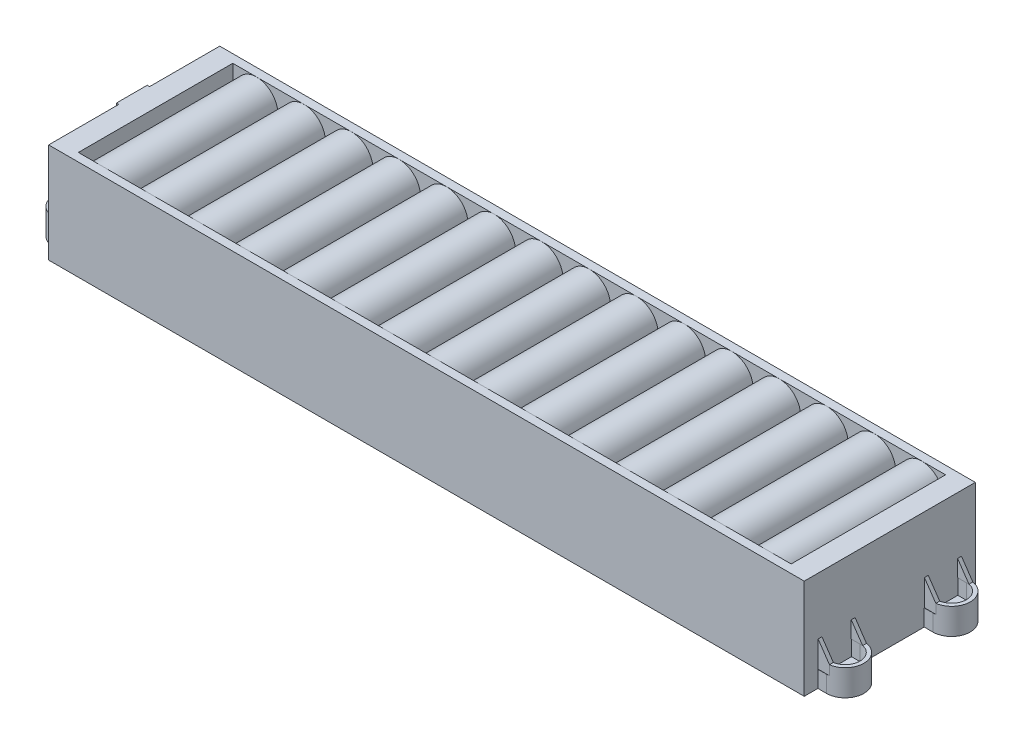
SolidWorks part; units mm, degrees
ref_plane "Front Plane" through (0, 0, 0) normal (0, 0, 1) x (1, 0, 0)
ref_plane "Top Plane" through (0, 0, 0) normal (0, 1, 0) x (1, 0, 0)
ref_plane "Right Plane" through (0, 0, 0) normal (1, 0, 0) x (0, 0, -1)
sketch "Sketch1" plane through (0, 0, 0) normal (0, 1, 0) x (1, 0, 0)
  line L1 (159, -36) -> (-159, -36)
  line L2 (159, -36) -> (159, 36)
  line L3 (159, 36) -> (-159, 36)
  line L4 (-159, -36) -> (-159, 36)
  line L5 (159, -36) -> (-159, 36) construction
  line L6 (159, 36) -> (-159, -36) construction
  point P0 (0, 0)
  dimension "D1" = 318
  dimension "D2" = 72
extrude "Boss-Extrude1" add sketch "Sketch1" along normal blind 42
sketch "Sketch2" plane through (0, 0, 0) normal (0, -1, 0) x (1, 0, 0)
  line L0 (162.625, 14.5) -> (159, 14.5)
  line L1 (159, 36) -> (159, -36) construction
  line L2 (162.625, 30.25) -> (159, 30.25)
  line L4 (162.625, 16.1) -> (159, 16.1)
  line L5 (162.625, 28.65) -> (159, 28.65)
  line L7 (159, 30.25) -> (159, 28.65)
  line L8 (159, 16.1) -> (159, 14.5)
  line L9 (162.625, -14.5) -> (159, -14.5)
  line L10 (159, -14.5) -> (159, -16.1)
  line L11 (159, -30.25) -> (162.625, -30.25)
  line L12 (159, -28.65) -> (162.625, -28.65)
  line L13 (162.625, -16.1) -> (159, -16.1)
  line L14 (159, -28.65) -> (159, -30.25)
  line L15 (-162.625, -14.5) -> (-159, -14.5)
  line L16 (-159, -36) -> (-159, 36) construction
  line L17 (-159, -14.5) -> (-159, -16.1)
  line L18 (-159, -30.25) -> (-162.625, -30.25)
  line L19 (-162.625, 14.5) -> (-159, 14.5)
  line L20 (-159, 14.5) -> (-159, 16.1)
  line L21 (-159, 30.25) -> (-162.625, 30.25)
  line L22 (-159, 28.65) -> (-162.625, 28.65)
  line L23 (-162.625, 16.1) -> (-159, 16.1)
  line L24 (-159, -28.65) -> (-162.625, -28.65)
  line L25 (-162.625, -16.1) -> (-159, -16.1)
  line L26 (-159, -28.65) -> (-159, -30.25)
  line L27 (-159, 28.65) -> (-159, 30.25)
  arc A0 (162.625, 14.5) -> (162.625, 30.25) centre (162.625, 22.375) ccw
  arc A1 (162.625, 16.1) -> (162.625, 28.65) centre (162.625, 22.375) ccw
  arc A2 (162.625, -30.25) -> (162.625, -14.5) centre (162.625, -22.375) ccw
  arc A3 (162.625, -28.65) -> (162.625, -16.1) centre (162.625, -22.375) ccw
  arc A4 (-162.625, 30.25) -> (-162.625, 14.5) centre (-162.625, 22.375) ccw
  arc A5 (-162.625, -14.5) -> (-162.625, -30.25) centre (-162.625, -22.375) ccw
  arc A6 (-162.625, 28.65) -> (-162.625, 16.1) centre (-162.625, 22.375) ccw
  arc A7 (-162.625, -16.1) -> (-162.625, -28.65) centre (-162.625, -22.375) ccw
  point P8 (159, 0)
  point P9 (170.5, 22.375)
  point P15 (170.5, -22.375)
  point P26 (-170.5, 22.375)
  point P28 (-170.5, -22.375)
  point P40 (-159, 0)
  dimension "D1" = 14.5
  dimension "D2" = 15.75
  dimension "D3" = 11.5
  dimension "D5" = 14.5
  dimension "D6" = 15.75
  dimension "D7" = 11.5
  dimension "D9" = 14.5
  dimension "D10" = 14.5
  dimension "D11" = 15.75
  dimension "D12" = 15.75
  dimension "D13" = 11.5
  dimension "D14" = 11.5
  dimension "D4" = 1.6
  dimension "D8" = 1.6
  dimension "D15" = 1.6
  dimension "D16" = 1.6
extrude "Boss-Extrude2" add sketch "Sketch2" against normal blind 11 separate body
sketch "Sketch3" plane through (0, 0, 0) normal (0, -1, 0) x (1, 0, 0)
  line L0 (159, 28.65) -> (159, 16.1)
  line L1 (159, 16.1) -> (162.625, 16.1)
  line L2 (162.625, 28.65) -> (159, 28.65)
  line L3 (161.825, 22.375) -> (165.075, 22.375) construction
  line L4 (161.825, 24.55) -> (165.075, 24.55)
  line L5 (161.825, 20.2) -> (165.075, 20.2)
  arc A0 (162.625, 28.65) -> (162.625, 16.1) centre (162.625, 22.375) cw
  arc A1 (161.825, 24.55) -> (161.825, 20.2) centre (161.825, 22.375) ccw
  arc A2 (165.075, 20.2) -> (165.075, 24.55) centre (165.075, 22.375) ccw
  arc A3 (162.625, 14.5) -> (162.625, 30.25) centre (162.625, 22.375) ccw construction
  point P13 (163.45, 22.375)
  point P18 (167.25, 22.375)
  point P19 (170.5, 22.375)
  dimension "D1" = 2.175
  dimension "D2" = 3.25
  dimension "D3" = 3.25
extrude "Boss-Extrude3" add sketch "Sketch3" against normal blind 4.5
mirror "Mirror5" about plane through (0, 0, 0) normal (1, 0, 0) of "Boss-Extrude3" second plane through (0, 0, 0) second plane normal (0, 0, 1)
sketch "Sketch4" plane through (0, 0, 0) normal (0, 0, 1) x (1, 0, 0)
  line L2 (-159, 42) -> (159, 42) construction
  line L3 (-159, 42) -> (-159, 0) construction
  line L10 (-131, 33) -> (-130, 33)
  line L11 (-130, 33) -> (-130, 42)
  line L12 (-159, 42) -> (159, 42) construction
  line L13 (-130, 42) -> (-150, 42)
  line L14 (-150, 42) -> (-150, 33)
  line L15 (-150, 33) -> (-149, 33)
  arc A0 (-131, 33) -> (-149, 33) centre (-140, 33) ccw
  point P2 (-140, 42)
  dimension "D1" = 18
  dimension "D2" = 19
  dimension "D3" = 1
  dimension "D4" = 1
extrude "Cut-Extrude1" cut sketch "Sketch4" against normal blind 32.5 and the other way blind 32.5
pattern_linear "LPattern1" count 15 spacing 20 along (1, 0, 0) of "Cut-Extrude1"
ref_plane "Plane1" through (0, 21, 0) normal (0, -1, 0) x (-1, 0, 0)
mirror "Mirror7" about plane through (0, 21, 0) normal (0, -1, 0) of "LPattern1", "Cut-Extrude1"
sketch "Sketch5" plane through (0, 0, 36) normal (0, 0, 1) x (1, 0, 0)
  line L0 (159, 11) -> (163.8, 11)
  line L1 (170.5, 11) -> (162.625, 11) construction
  line L2 (163.8, 11) -> (159, 18)
  line L3 (159, 42) -> (159, 0) construction
  line L4 (159, 18) -> (159, 11)
  dimension "D1" = 7
  dimension "D2" = 4.8
extrude "Boss-Extrude4" add sketch "Sketch5" against normal through all
sketch "Sketch6" plane through (0, 42, 0) normal (0, 1, 0) x (1, 0, 0)
  line L0 (159, -36) -> (159, 36) construction
  line L1 (159, -36) -> (163.8, -36)
  line L2 (159, -36) -> (159, -30.1618)
  line L3 (159, -30.1618) -> (163.8, -30.1618)
  line L4 (163.8, -36) -> (163.8, -30.1618)
  line L5 (163.8, -28.539) -> (159, -28.539)
  line L6 (163.8, -28.539) -> (163.8, -16.211)
  line L7 (163.8, -16.211) -> (159, -16.211)
  line L8 (159, -28.539) -> (159, -16.211)
  line L9 (163.8, -16.211) -> (163.8, -28.539) construction
  line L10 (159, 36) -> (159, -36) construction
  line L11 (163.8, -14.5882) -> (159, -14.5882)
  line L12 (163.8, -14.5882) -> (163.8, 14.5882)
  line L13 (163.8, 14.5882) -> (159, 14.5882)
  line L14 (159, -14.5882) -> (159, 14.5882)
  line L15 (163.8, 14.5882) -> (163.8, -14.5882) construction
  line L16 (163.8, 28.539) -> (163.8, 16.211) construction
  line L17 (163.8, 16.211) -> (159, 16.211)
  line L18 (163.8, 16.211) -> (163.8, 28.539)
  line L19 (163.8, 28.539) -> (159, 28.539)
  line L20 (159, 16.211) -> (159, 28.539)
  line L22 (159, 36) -> (163.8, 36)
  line L23 (159, 36) -> (159, 30.1618)
  line L24 (159, 30.1618) -> (163.8, 30.1618)
  line L25 (163.8, 36) -> (163.8, 30.1618)
  arc A0 (162.625, -28.65) -> (162.625, -16.1) centre (162.625, -22.375) ccw construction
  arc A1 (163.8, 14.5882) -> (163.8, 30.1618) centre (162.625, 22.375) ccw construction
  arc A2 (162.625, 16.1) -> (162.625, 28.65) centre (162.625, 22.375) ccw construction
extrude "Cut-Extrude2" cut sketch "Sketch6" against normal blind 35
sketch "Sketch7" plane through (-159, 0, 0) normal (-1, 0, 0) x (0, 0, 1)
  line L0 (-36, 42) -> (36, 42) construction
  line L1 (-6.5, 42) -> (6.5, 42)
  line L2 (-6.5, 42) -> (-6.5, 32)
  line L3 (-6.5, 32) -> (6.5, 32)
  line L4 (6.5, 42) -> (6.5, 32)
  point P6 (0, 42)
  point P7 (0, 42)
  dimension "D1" = 13
  dimension "D2" = 10
extrude "Boss-Extrude5" add sketch "Sketch7" along normal blind 1
equation "\"D1@Sketch2\"=29/2"
equation "\"D1@Sketch3\"=4.35/2"
equation "\"D2@Sketch3\"=7.6-2*\"D1@Sketch3\""
equation "\"D5@Sketch2\"=\"D1@Sketch2\""
equation "\"D6@Sketch2\"=\"D2@Sketch2\""
equation "\"D7@Sketch2\"=\"D3@Sketch2\""
equation "\"D9@Sketch2\"=\"D1@Sketch2\""
equation "\"D10@Sketch2\"=\"D1@Sketch2\""
equation "\"D11@Sketch2\"=\"D2@Sketch2\""
equation "\"D12@Sketch2\"=\"D2@Sketch2\""
equation "\"D13@Sketch2\"=\"D3@Sketch2\""
equation "\"D14@Sketch2\"=\"D3@Sketch2\""
